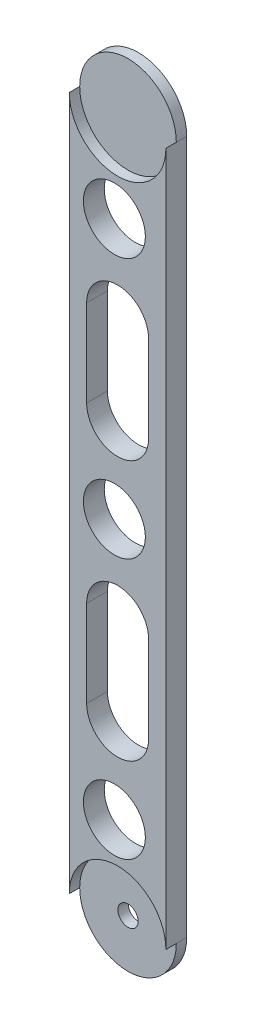
SolidWorks part; units mm, degrees
ref_plane "Plan de face" through (0, 0, 0) normal (0, 0, 1) x (1, 0, 0)
ref_plane "Plan de dessus" through (0, 0, 0) normal (0, 1, 0) x (1, 0, 0)
ref_plane "Plan de droite" through (0, 0, 0) normal (1, 0, 0) x (0, 0, -1)
sketch "Esquisse1" plane through (0, 0, 0) normal (0, 0, 1) x (1, 0, 0)
  line L1 (-9.9585, 27.1869) -> (17.8915, 27.1869)
  line L2 (-9.9585, 27.1869) -> (-9.9585, -172.8131)
  line L3 (-9.9585, -172.8131) -> (17.8915, -172.8131)
  line L4 (17.8915, 27.1869) -> (17.8915, -172.8131)
  arc A0 (-9.9585, -172.8131) -> (17.8915, -172.8131) centre (3.9665, -172.8131) ccw
  arc A1 (17.8915, 27.1869) -> (-9.9585, 27.1869) centre (3.9665, 27.1869) ccw
  dimension "D1" = 27.85
  dimension "D2" = 200
extrude "Boss.-Extru.1" add sketch "Esquisse1" along normal blind 6 contours L4 L1 L2 L3 | L3 A0 | L1 A1
sketch "Esquisse2" plane through (0, 0, 6) normal (0, 0, 1) x (1, 0, 0)
  circle A0 centre (3.9665, -172.8131) radius 13.925
extrude "Enlèv. mat.-Extru.1" cut sketch "Esquisse2" against normal blind 3
sketch "Esquisse3" plane through (0, 0, 3) normal (0, 0, 1) x (1, 0, 0)
  circle A0 centre (3.9665, -172.8131) radius 2.925
  dimension "D1" = 5.85
extrude "Enlèv. mat.-Extru.2" cut sketch "Esquisse3" against normal blind 3
sketch "Esquisse4" plane through (0, 0, 0) normal (0, 0, -1) x (-1, 0, 0)
  circle A0 centre (-3.9665, 27.1869) radius 13.925
sketch "Esquisse5" plane through (0, 0, 6) normal (0, 0, 1) x (1, 0, 0)
  circle A0 centre (3.9665, 27.1869) radius 13.925
extrude "Enlèv. mat.-Extru.3" cut sketch "Esquisse5" against normal blind 3
sketch "Esquisse6" plane through (0, 0, 0) normal (0, 0, -1) x (-1, 0, 0)
  line L0 (9.9585, 27.1869) -> (9.9585, -172.8131) construction
  line L1 (-12.8915, -22.8131) -> (4.9585, -22.8131)
  line L2 (-12.8915, -22.8131) -> (-12.8915, -47.8131)
  line L3 (-12.8915, -47.8131) -> (4.9585, -47.8131)
  line L4 (4.9585, -22.8131) -> (4.9585, -47.8131)
  line L5 (-12.8915, -97.8131) -> (4.9585, -97.8131)
  line L6 (-12.8915, -97.8131) -> (-12.8915, -122.8131)
  line L7 (-12.8915, -122.8131) -> (4.9585, -122.8131)
  line L8 (4.9585, -97.8131) -> (4.9585, -122.8131)
  line L9 (-17.8915, 27.1869) -> (-17.8915, -172.8131) construction
  circle A0 centre (-3.0406, 2.1869) radius 8.925
  circle A1 centre (-3.0406, -72.8131) radius 8.925
  circle A2 centre (-3.0406, -147.8131) radius 8.925
  arc A3 (-12.8915, -22.8131) -> (4.9585, -22.8131) centre (-3.9665, -22.8131) cw
  arc A4 (4.9585, -47.8131) -> (-12.8915, -47.8131) centre (-3.9665, -47.8131) cw
  arc A5 (-12.8915, -97.8131) -> (4.9585, -97.8131) centre (-3.9665, -97.8131) cw
  arc A6 (4.9585, -122.8131) -> (-12.8915, -122.8131) centre (-3.9665, -122.8131) cw
  circle A7 centre (-3.9665, -172.8131) radius 2.925 construction
  dimension "D3" = 17.85
  dimension "D4" = 17.85
  dimension "D5" = 17.85
  dimension "D1" = 5
  dimension "D2" = 5
  dimension "D6" = 5
  dimension "D7" = 5
  dimension "D8" = 25
  dimension "D9" = 25
  dimension "D10" = 50
  dimension "D11" = 25
  dimension "D12" = 25
  dimension "D13" = 50
  dimension "D14" = 25
extrude "Enlèv. mat.-Extru.4" cut sketch "Esquisse6" against normal blind 10 contours A0 | A3 L1 | L4 L1 L2 L3 | A4 L3 | A1 | L8 L5 L6 L7 | A5 L5 | A6 L7 | A2
